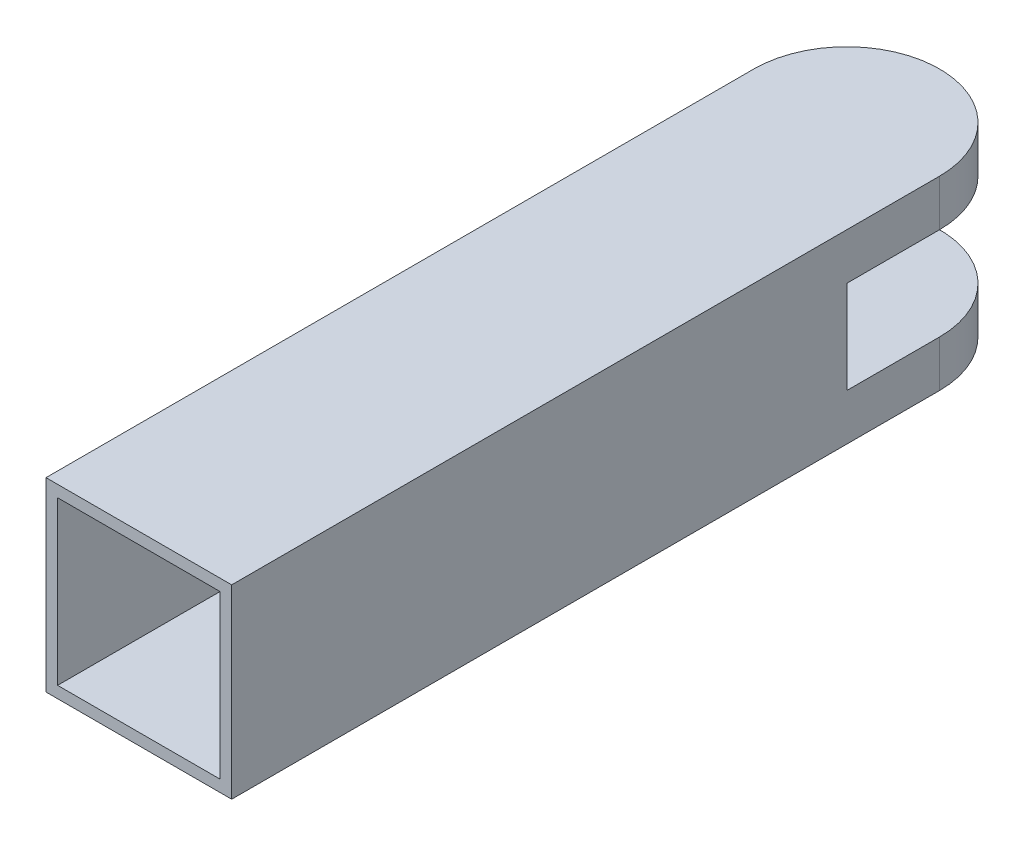
SolidWorks part; units mm, degrees
ref_plane "Front" through (0, 0, 0) normal (0, 0, 1) x (1, 0, 0)
ref_plane "Top" through (0, 0, 0) normal (0, 1, 0) x (1, 0, 0)
ref_plane "Right" through (0, 0, 0) normal (1, 0, 0) x (0, 0, -1)
sketch "草图1" plane through (0, 0, 0) normal (0, 0, 1) x (1, 0, 0)
  line L0 (-19.8866, 0) -> (0, 0) construction
  line L1 (0, 0) -> (0, 23.0931) construction
  line L3 (-8, 8) -> (8, 8)
  line L4 (-8, 8) -> (-8, -8)
  line L5 (-8, -8) -> (8, -8)
  line L6 (8, 8) -> (8, -8)
  line L7 (-7, 7) -> (7, 7)
  line L8 (-7, 7) -> (-7, -7)
  line L9 (-7, -7) -> (7, -7)
  line L10 (7, 7) -> (7, -7)
  dimension "D1" = 16
  dimension "D2" = 16
  dimension "D3" = 8
  dimension "D4" = 8
  dimension "D5" = 14
  dimension "D6" = 7
  dimension "D7" = 14
  dimension "D8" = 7
extrude "凸台-拉伸1" add sketch "草图1" along normal blind 52
sketch "草图2" plane through (0, 0, 0) normal (0, 0, -1) x (-1, 0, 0)
  line L1 (-8, 8) -> (8, 8)
  line L2 (-8, 8) -> (-8, -8)
  line L3 (-8, -8) -> (8, -8)
  line L4 (8, 8) -> (8, -8)
extrude "凸台-拉伸2" add sketch "草图2" along normal blind 1
sketch "草图3" plane through (0, 0, -1) normal (0, 0, -1) x (-1, 0, 0)
  line L1 (-8, 8) -> (8, 8)
  line L2 (-8, 8) -> (-8, -8)
  line L3 (-8, -8) -> (8, -8)
  line L4 (8, 8) -> (8, -8)
extrude "凸台-拉伸3" add sketch "草图3" along normal blind 16
sketch "草图4" plane through (0, -8, 0) normal (0, -1, 0) x (1, 0, 0)
  line L2 (-8, -9) -> (-8, -21.564)
  line L3 (-8, -21.564) -> (8, -21.564)
  line L4 (8, -9) -> (8, -21.564)
  arc A0 (-8, -9) -> (8, -9) centre (0, -9) ccw
extrude "切除-拉伸1" cut sketch "草图4" against normal blind 16
sketch "草图5" plane through (8, 0, 0) normal (1, 0, 0) x (0, 0, -1)
  line L0 (0, 0) -> (24.9394, 0) construction
  line L1 (17, 8) -> (17, -8) construction
  line L3 (17, 4) -> (1, 4)
  line L4 (17, 4) -> (17, -4)
  line L5 (17, -4) -> (1, -4)
  line L6 (1, 4) -> (1, -4)
  dimension "D1" = 16
  dimension "D2" = 8
  dimension "D3" = 4
extrude "切除-拉伸2" cut sketch "草图5" against normal through all
